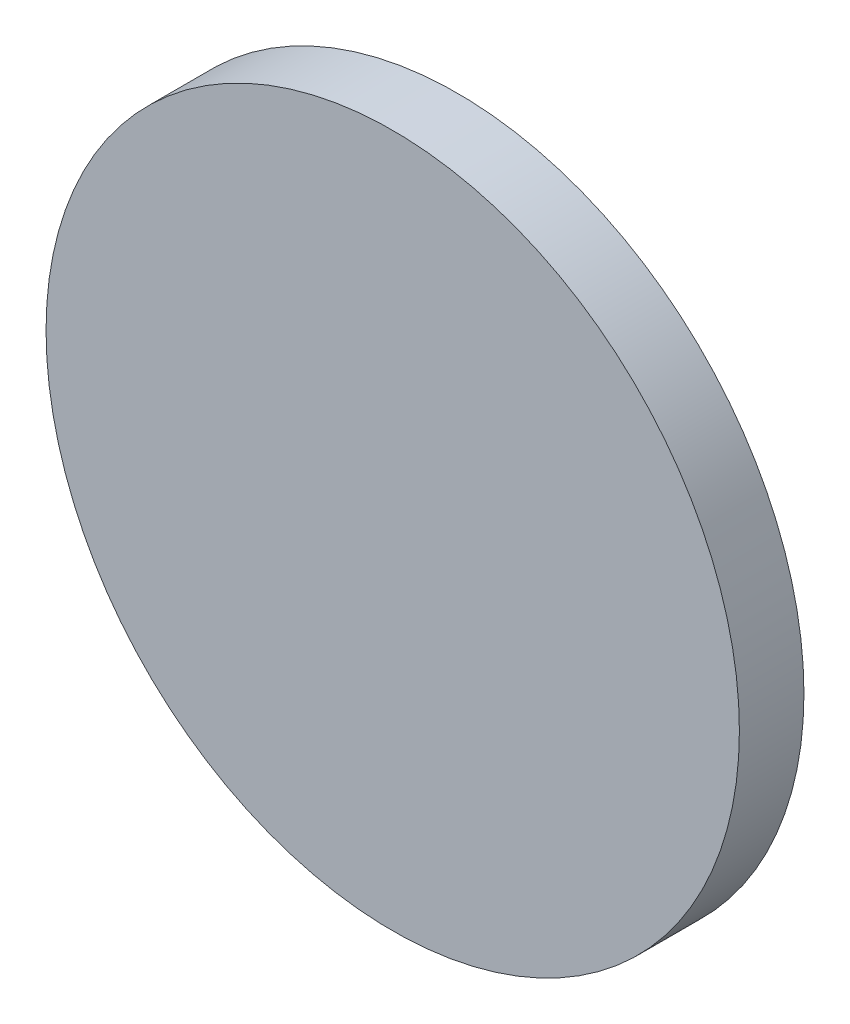
SolidWorks part; units mm, degrees
ref_plane "Front Plane" through (0, 0, 0) normal (0, 0, 1) x (1, 0, 0)
ref_plane "Top Plane" through (0, 0, 0) normal (0, 1, 0) x (1, 0, 0)
ref_plane "Right Plane" through (0, 0, 0) normal (1, 0, 0) x (0, 0, -1)
sketch "Sketch1" plane through (0, 0, 0) normal (0, 0, 1) x (1, 0, 0)
  circle A0 centre (-70.2259, 36.7961) radius 9.4
  dimension "D1" = 18.8
extrude "Boss-Extrude1" add sketch "Sketch1" along normal blind 1.75
